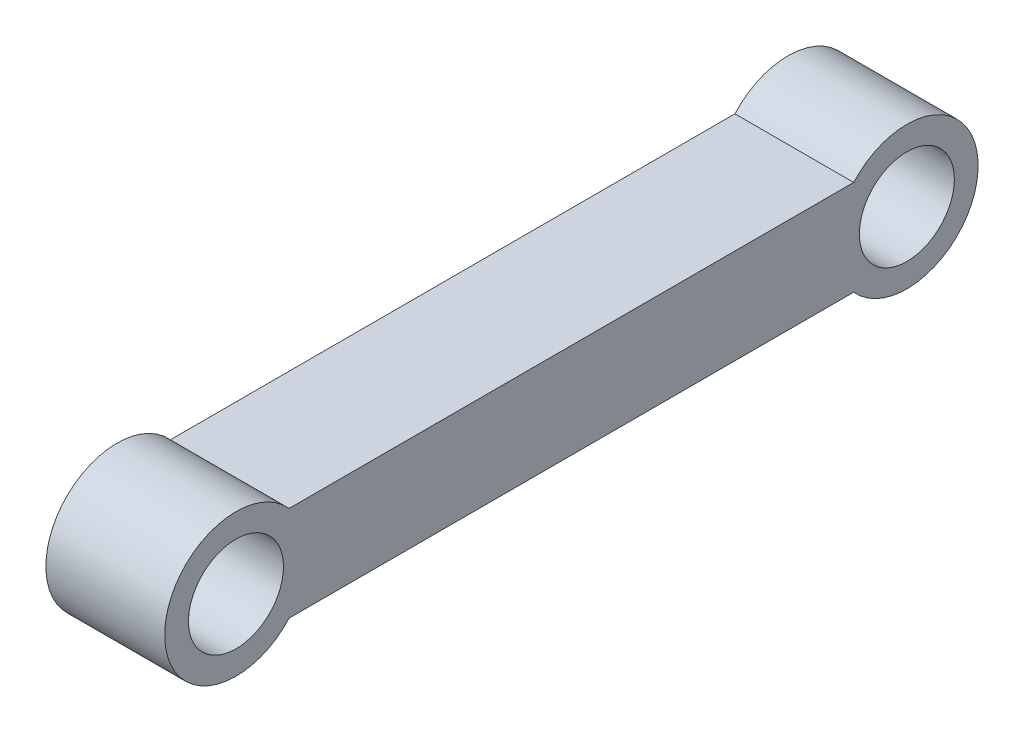
SolidWorks part; units mm, degrees
material "Thornel Mat VMA"
ref_plane "Front Plane" through (0, 0, 0) normal (0, 0, 1) x (1, 0, 0)
ref_plane "Top Plane" through (0, 0, 0) normal (0, 1, 0) x (1, 0, 0)
ref_plane "Right Plane" through (0, 0, 0) normal (1, 0, 0) x (0, 0, -1)
sketch "LinkFrame" plane through (0, 0, 0) normal (1, 0, 0) x (0, 0, -1)
  line L0 (-304.9655, -226.2633) -> (259.6545, -226.2633) construction
  line L1 (-260.2442, -186.2633) -> (214.9331, -186.2633)
  line L2 (-260.2442, -266.2633) -> (214.9331, -266.2633)
  arc A1 (214.9331, -266.2633) -> (214.9331, -186.2633) centre (259.6545, -226.2633) ccw
  arc A2 (-260.2442, -186.2633) -> (-260.2442, -266.2633) centre (-304.9655, -226.2633) ccw
  circle A5 centre (-304.9655, -226.2633) radius 40
  circle A6 centre (259.6545, -226.2633) radius 40
  dimension "D1" = 120
  dimension "D2" = 120
  dimension "D5" = 80
  dimension "D6" = 80
  dimension "D3" = 564.62
  dimension "D4" = 80
  dimension "D7" = 44.7214
  dimension "D8" = 44.7214
extrude "Boss-Extrude1" add sketch "LinkFrame" along normal blind 100
equation "\"D1@LinkFrame\" = 1.5 * \"HoleMountDiameter@PrintingPress.Assembly\""
equation "\"D2@LinkFrame\" = 1.5 * \"HoleMountDiameter@PrintingPress.Assembly\""
equation "\"LinkLength\"= 54cm + 2.462cm"
equation "\"D3@LinkFrame\" = \"LinkLength\""
equation "\"D4@LinkFrame\" = \"HoleMountDiameter@PrintingPress.Assembly\""
equation "\"D5@LinkFrame\"=\"HoleMountDiameter@PrintingPress.Assembly\""
equation "\"D6@LinkFrame\"=\"HoleMountDiameter@PrintingPress.Assembly\""
equation "\"D1@Boss-Extrude1\"=\"RivetLength@PrintingPress.Assembly\""
